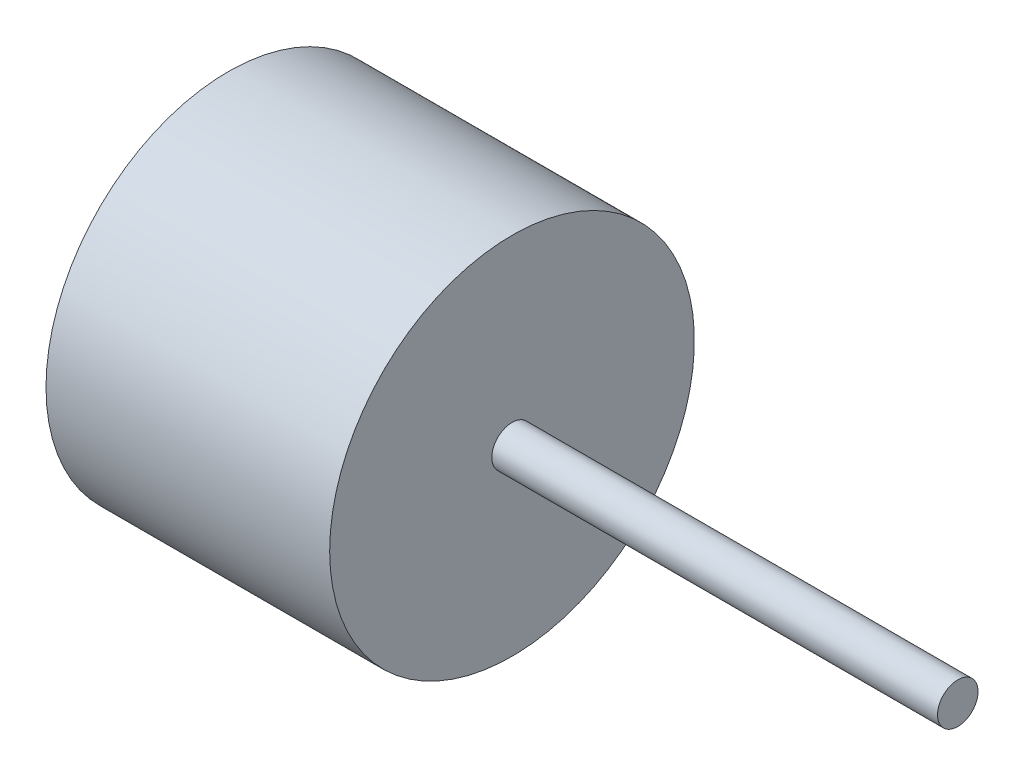
SolidWorks part; units mm, degrees
ref_plane "Plan de face" through (0, 0, 0) normal (0, 0, 1) x (1, 0, 0)
ref_plane "Plan de dessus" through (0, 0, 0) normal (0, 1, 0) x (1, 0, 0)
ref_plane "Plan de droite" through (0, 0, 0) normal (1, 0, 0) x (0, 0, -1)
sketch "Esquisse1" plane through (0, 0, 0) normal (0, 0, 1) x (1, 0, 0)
  line L0 (-38.2151, 0) -> (28.0969, 0) construction
  line L1 (22, 0) -> (22, 1)
  line L2 (22, 1) -> (0, 1)
  line L3 (0, 1) -> (0, 9)
  line L4 (0, 9) -> (-14, 9)
  line L5 (-14, 9) -> (-14, 0)
  line L6 (-14, 0) -> (22, 0)
  dimension "D1" = 2
  dimension "D2" = 18
  dimension "D3" = 22
  dimension "D4" = 14
revolve "Révolution1" add sketch "Esquisse1" angle 360 about L0
